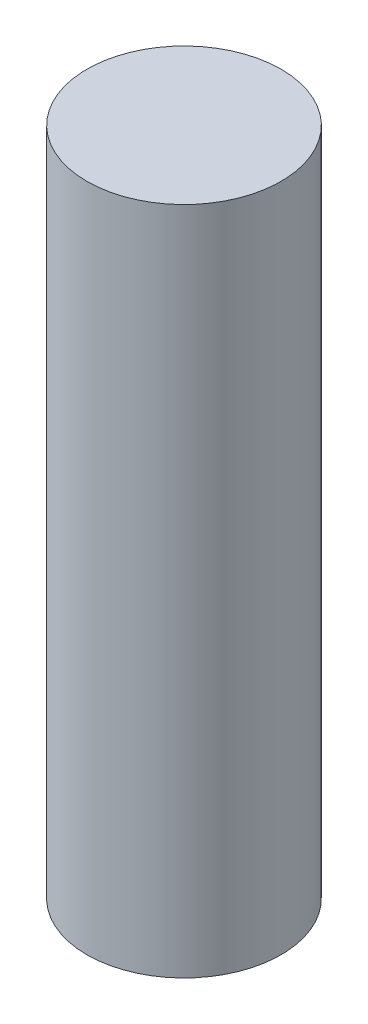
SolidWorks part; units mm, degrees
ref_plane "Front Plane" through (0, 0, 0) normal (0, 0, 1) x (1, 0, 0)
ref_plane "Top Plane" through (0, 0, 0) normal (0, 1, 0) x (1, 0, 0)
ref_plane "Right Plane" through (0, 0, 0) normal (1, 0, 0) x (0, 0, -1)
sketch "Sketch1" plane through (0, 0, 0) normal (0, 1, 0) x (1, 0, 0)
  circle A0 centre (2.9998, -2.8438) radius 3.683
  dimension "D1" = 7.366
extrude "Boss-Extrude1" add sketch "Sketch1" along normal blind 25.4
